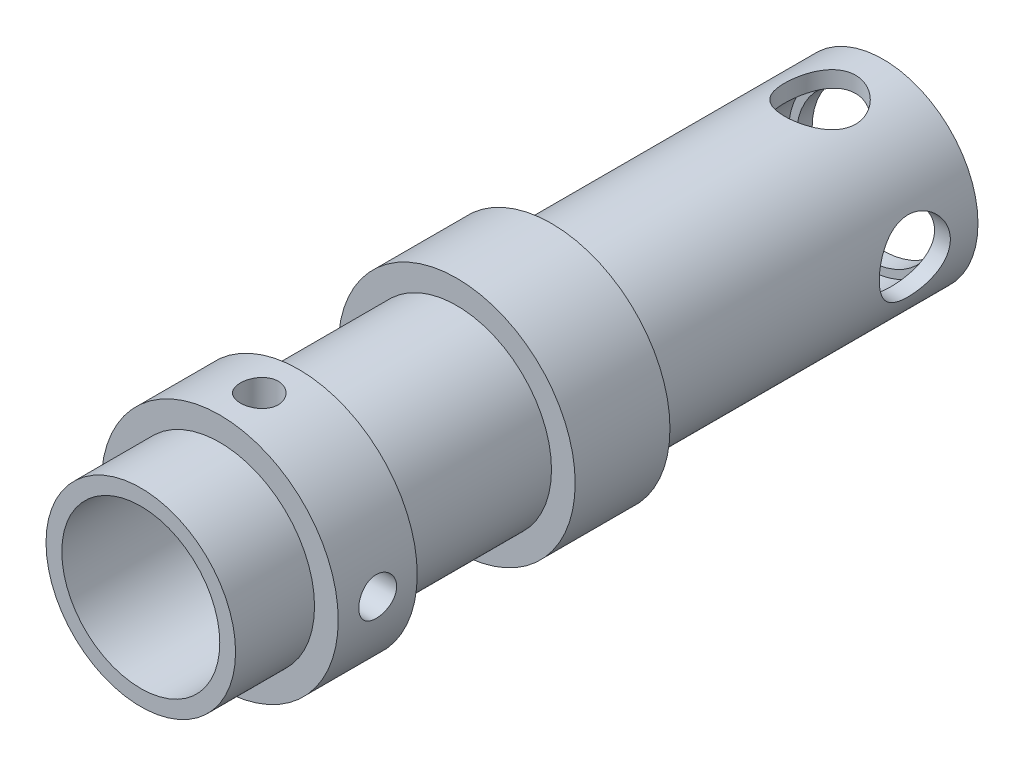
SolidWorks part; units mm, degrees
material "Alliage 1060"
ref_plane "Plan de face" through (0, 0, 0) normal (0, 0, 1) x (1, 0, 0)
ref_plane "Plan de dessus" through (0, 0, 0) normal (0, 1, 0) x (1, 0, 0)
ref_plane "Plan de droite" through (0, 0, 0) normal (1, 0, 0) x (0, 0, -1)
sketch "Esquisse1" plane through (0, 0, 0) normal (0, 0, 1) x (1, 0, 0)
  circle A0 centre (0, 0) radius 5
  circle A1 centre (0, 0) radius 6
  dimension "D1" = 10
  dimension "D2" = 12
extrude "Boss.-Extru.1" add sketch "Esquisse1" along normal blind 21
sketch "Esquisse2" plane through (0, 0, 0) normal (0, 0, -1) x (-1, 0, 0)
  circle A0 centre (0, 0) radius 4.5
  circle A1 centre (0, 0) radius 6
  dimension "D1" = 12
  dimension "D2" = 9
extrude "Boss.-Extru.2" add sketch "Esquisse2" against normal blind 1
sketch "Esquisse3" plane through (0, 0, 21) normal (0, 0, 1) x (1, 0, 0)
  circle A0 centre (0, 0) radius 7.5
  circle A1 centre (0, 0) radius 5
  dimension "D1" = 10
  dimension "D2" = 15
extrude "Boss.-Extru.3" add sketch "Esquisse3" along normal blind 6
sketch "Esquisse4" plane through (0, 0, 27) normal (0, 0, 1) x (1, 0, 0)
  circle A0 centre (0, 0) radius 5
  circle A1 centre (0, 0) radius 6
  dimension "D1" = 10
  dimension "D2" = 12
extrude "Boss.-Extru.4" add sketch "Esquisse4" along normal blind 10
sketch "Esquisse7" plane through (0, 0, 37) normal (0, 0, 1) x (1, 0, 0)
  circle A0 centre (0, 0) radius 5
  circle A1 centre (0, 0) radius 7.5
  dimension "D1" = 10
  dimension "D2" = 15
extrude "Boss.-Extru.7" add sketch "Esquisse7" along normal blind 5
sketch "Esquisse8" plane through (0, 0, 42) normal (0, 0, 1) x (1, 0, 0)
  circle A0 centre (0, 0) radius 5
  circle A1 centre (0, 0) radius 6
  dimension "D1" = 10
  dimension "D2" = 12
extrude "Boss.-Extru.8" add sketch "Esquisse8" along normal blind 5
hole_wizard "Dégagement M22" positions "Esquisse3D5" profile "Esquisse13" hole size "M2" standard "ISO" end condition through all
sketch3d "Esquisse3D5"
  point P0 (0, -7.5, 39.5)
  point P8 (7.5, 0, 39.5)
  dimension "D1" = 2.5
  dimension "D2" = 2.5
sketch "Esquisse13" plane through (0, -7.5, 39.5) normal (1, 0, 0) x (0, 0, -1)
  line L0 (0, 0) -> (0, 15)
  line L1 (0, 15) -> (1.2, 15)
  line L2 (1.2, 15) -> (1.2, 0)
  line L5 (1.2, 0) -> (0, 0)
  line L11 (0, -6.35) -> (0, 107.95) construction
  dimension "Diamètre du perçage jusqu'au prochain" = 2.4
  dimension "Profondeur du perçage jusqu'au prochain" = 15
hole_wizard "Dégagement M41" positions "Esquisse3D6" profile "Esquisse14" hole size "M4" standard "ISO" end condition through all
sketch3d "Esquisse3D6"
  point P0 (6, 0, 4)
  point P2 (0, 6, 4)
  dimension "D1" = 4
  dimension "D2" = 4
sketch "Esquisse14" plane through (6, 0, 4) normal (0, 1, 0) x (0, 0, -1)
  line L0 (0, 0) -> (0, 13.5)
  line L1 (0, 13.5) -> (2.25, 13.5)
  line L2 (2.25, 13.5) -> (2.25, 0)
  line L5 (2.25, 0) -> (0, 0)
  line L11 (0, -6.35) -> (0, 107.95) construction
  dimension "Diamètre du perçage jusqu'au prochain" = 4.5
  dimension "Profondeur du perçage jusqu'au prochain" = 13.5
